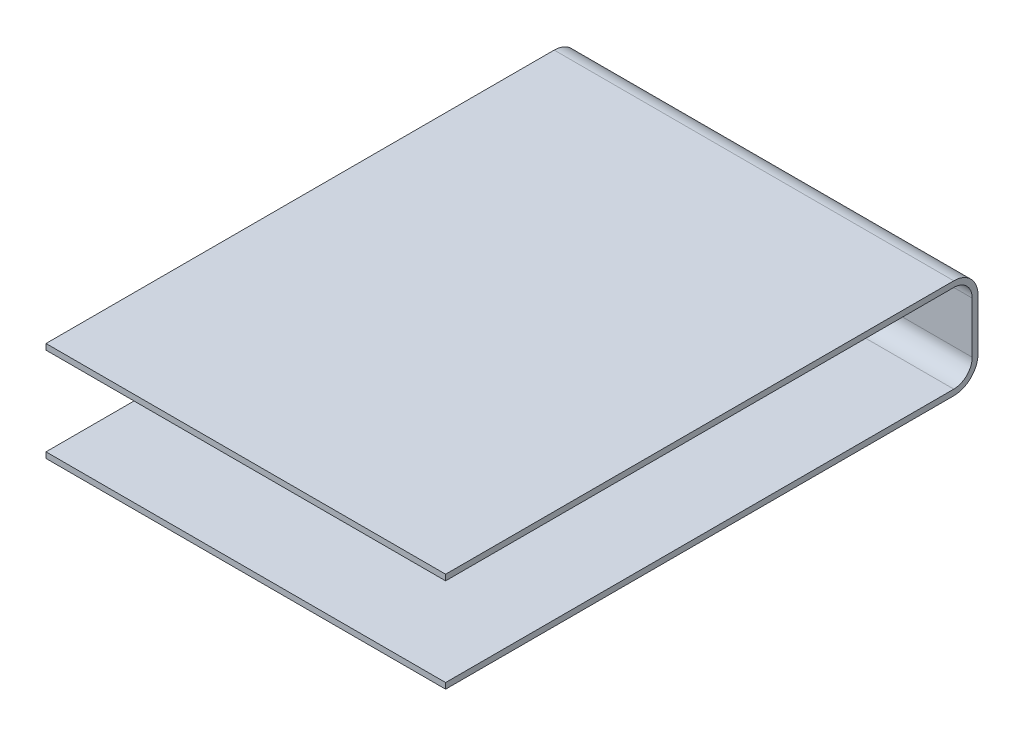
SolidWorks part; units mm, degrees
ref_plane "Front Plane" through (0, 0, 0) normal (0, 0, 1) x (1, 0, 0)
ref_plane "Top Plane" through (0, 0, 0) normal (0, 1, 0) x (1, 0, 0)
ref_plane "Right Plane" through (0, 0, 0) normal (1, 0, 0) x (0, 0, -1)
sketch "Sketch1" plane through (0, 0, 0) normal (1, 0, 0) x (0, 0, -1)
  line L0 (0, 0) -> (-9652, 0)
  line L1 (-9652, 0) -> (-9652, -110)
  line L2 (0, 1672) -> (-9652, 1672)
  line L3 (350, 1322) -> (350, 350)
  line L4 (-9652, -110) -> (0, -110)
  line L5 (-9652, 1672) -> (-9652, 1782)
  line L6 (-9652, 1782) -> (0, 1782)
  line L7 (460, 1322) -> (460, 350)
  arc A0 (0, 1672) -> (350, 1322) centre (0, 1322) cw
  arc A1 (0, 0) -> (350, 350) centre (0, 350) ccw
  arc A2 (0, 1782) -> (460, 1322) centre (0, 1322) cw
  arc A3 (0, -110) -> (460, 350) centre (0, 350) ccw
  dimension "D1" = 9652
  dimension "D3" = 460
  dimension "D4" = 350
  dimension "D2" = 110
  dimension "D5" = 972
  dimension "D6" = 972
extrude "Boss-Extrude1" add sketch "Sketch1" against normal blind 7590
sketch "Sketch4" plane through (0, 1672, 0) normal (0, -1, 0) x (1, 0, 0)
  line L1 (-7590, 0) -> (-7590, 9652) construction
  line L2 (-7090, 8352) -> (-500, 8352)
  line L3 (0, 0) -> (0, 9652) construction
  arc A0 (-7090, 8352) -> (-7590, 7852) centre (-7090, 7852) ccw
  arc A1 (-500, 8352) -> (0, 7852) centre (-500, 7852) cw
sketch "Sketch5" plane through (0, -110, 0) normal (0, -1, 0) x (1, 0, 0)
  line L1 (-7590, 6652) -> (-7590, 9652)
  line L2 (-7590, 9652) -> (-7590, 6652)
  line L4 (-6720, 6652) -> (-6720, 802)
  line L5 (-6720, 802) -> (-870, 802)
  line L6 (-870, 802) -> (-870, 6652)
  line L7 (-870, 6652) -> (-6720, 6652)
